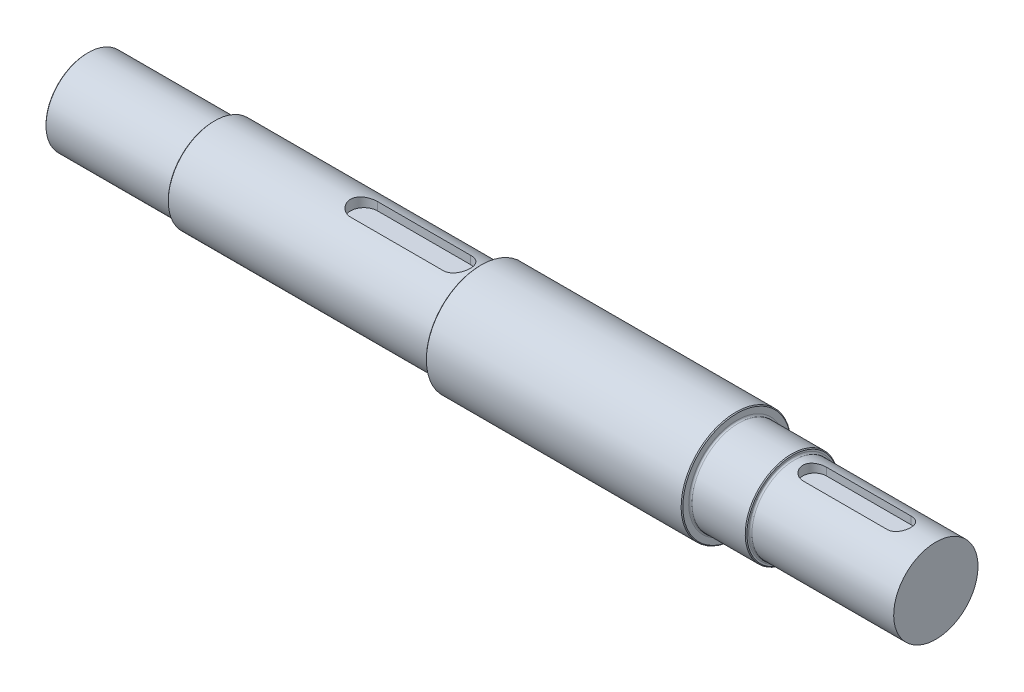
SolidWorks part; units mm, degrees
material "AISI 1045 Steel, cold drawn"
ref_plane "Front Plane" through (0, 0, 0) normal (0, 0, 1) x (1, 0, 0)
ref_plane "Top Plane" through (0, 0, 0) normal (0, 1, 0) x (1, 0, 0)
ref_plane "Right Plane" through (0, 0, 0) normal (1, 0, 0) x (0, 0, -1)
sketch "Sketch1" plane through (0, 0, 0) normal (0, 0, 1) x (1, 0, 0)
  line L0 (-113.7081, 0) -> (-113.7081, 25)
  line L1 (-113.7081, 25) -> (-38.7081, 25)
  line L2 (-38.7081, 25) -> (-38.7081, 27.5)
  line L3 (-38.7081, 27.5) -> (119.2919, 27.5)
  line L4 (119.2919, 27.5) -> (119.2919, 32.5)
  line L5 (119.2919, 32.5) -> (271.2919, 32.5)
  line L6 (271.2919, 32.5) -> (271.2919, 27.5)
  line L7 (271.2919, 27.5) -> (304.2919, 27.5)
  line L8 (304.2919, 27.5) -> (304.2919, 25)
  line L9 (178.8194, 0) -> (-113.7081, 0)
  line L10 (304.2919, 25) -> (389.2919, 25)
  line L11 (389.2919, 25) -> (389.2919, 0)
  line L12 (389.2919, 0) -> (178.8194, 0)
  dimension "D1" = 25
  dimension "D2" = 75
  dimension "D3" = 27.5
  dimension "D4" = 32.5
  dimension "D5" = 27.5
  dimension "D6" = 25
  dimension "D7" = 158
  dimension "D8" = 152
  dimension "D9" = 33
  dimension "D10" = 85
revolve "Revolve1" add sketch "Sketch1" angle 360 about L9
chamfer "Chamfer1" distance 0.5 angle 45 5 edges at (304.2919, 27.5, 0) (271.2919, 32.5, 0) (119.2919, 32.5, 0) (-38.7081, 27.5, 0) (-113.7081, 25, 0)
fillet "Fillet1" radius 1 4 edges at (304.2919, 25, 0) (271.2919, 27.5, 0) (119.2919, 27.5, 0) (-38.7081, 25, 0)
ref_plane "Plane1" through (0, 27.5, 0) normal (0, 1, 0) x (1, 0, 0)
ref_plane "Plane2" through (0, 25, 0) normal (0, 1, 0) x (1, 0, 0)
sketch "Sketch3" plane through (0, 27.5, 0) normal (0, 1, 0) x (1, 0, 0)
  line L0 (50.3281, 0) -> (105.3281, 0) construction
  line L1 (50.3281, 8) -> (105.3281, 8)
  line L2 (50.3281, -8) -> (105.3281, -8)
  arc A0 (50.3281, 8) -> (50.3281, -8) centre (50.3281, 0) ccw
  arc A1 (105.3281, -8) -> (105.3281, 8) centre (105.3281, 0) ccw
  point P3 (77.8281, 0)
  dimension "D1" = 16
  dimension "D2" = 55
sketch "Sketch4" plane through (0, 25, 0) normal (0, 1, 0) x (1, 0, 0)
  line L0 (317.4353, 0) -> (367.4353, 0) construction
  line L1 (317.4353, 7) -> (367.4353, 7)
  line L2 (317.4353, -7) -> (367.4353, -7)
  arc A0 (317.4353, 7) -> (317.4353, -7) centre (317.4353, 0) ccw
  arc A1 (367.4353, -7) -> (367.4353, 7) centre (367.4353, 0) ccw
  point P2 (342.4353, 0)
  dimension "D1" = 14
  dimension "D2" = 50
extrude "Cut-Extrude1" cut sketch "Sketch3" against normal blind 6 contours L2 A1 L1 A0
extrude "Cut-Extrude2" cut sketch "Sketch4" against normal blind 5.5 contours L2 A1 L1 A0
